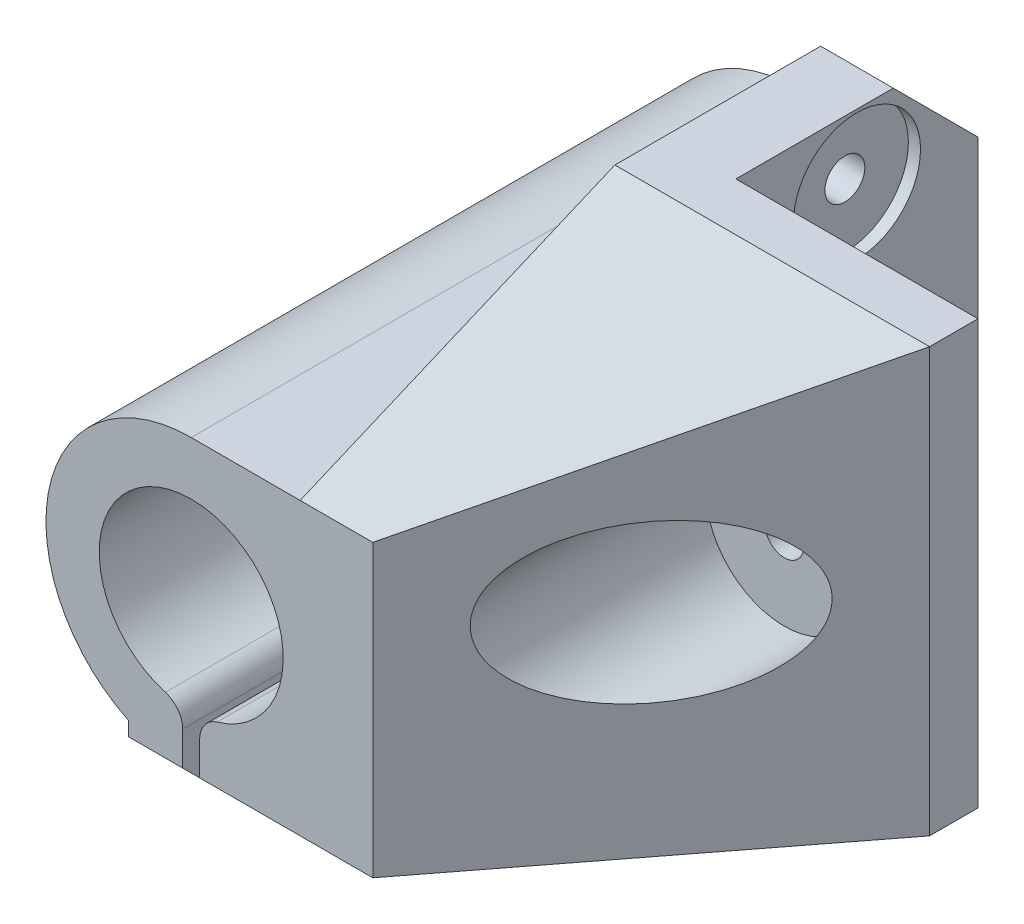
SolidWorks part; units mm, degrees
ref_plane "Plano frontal" through (0, 0, 0) normal (0, 0, 1) x (1, 0, 0)
ref_plane "Plano superior" through (0, 0, 0) normal (0, 1, 0) x (1, 0, 0)
ref_plane "Plano direito" through (0, 0, 0) normal (1, 0, 0) x (0, 0, -1)
sketch "Esboço1" plane through (0, 0, 0) normal (0, 0, 1) x (1, 0, 0)
  line L0 (-10, 11) -> (-10, -24) construction
  line L1 (-35, -24) -> (-35, -31) construction
  line L2 (0, 0) -> (0, 11)
  line L3 (0, -24) -> (0, 0)
  line L4 (-35.7, -19.5677) -> (-35.7, -31)
  line L5 (-34.3, -19.5677) -> (-34.3, -31)
  line L6 (-35, -12) -> (-24.5731, -12) construction
  line L7 (-40.2, -22.8148) -> (-40.2, -31)
  line L8 (-29.8, -24) -> (-29.8, -31)
  line L9 (-34.3, -19.65) -> (-34.3, -31) construction
  line L10 (-26, 0) -> (-35, 0)
  line L12 (-35.7, -19.65) -> (-35.7, -31) construction
  line L13 (-40.2, -19.65) -> (-40.2, -31) construction
  line L14 (-29.8, -19.65) -> (-29.8, -31) construction
  line L15 (-35, -19.65) -> (-35, -31) construction
  line L16 (-29.8, -24) -> (0, -24)
  line L17 (-29.8, -31) -> (-34.3, -31)
  line L18 (-35.7, -31) -> (-40.2, -31)
  line L19 (0, 11) -> (-26, 11)
  line L20 (-26, 11) -> (-26, 0)
  arc A0 (-35, 0) -> (-40.2, -22.8148) centre (-35, -12) ccw
  arc A1 (-34.3, -19.5677) -> (-35.7, -19.5677) centre (-35, -12) ccw
  circle A2 centre (-10, -6.5) radius 1.6
  point P17 (-10, -6.5)
  dimension "D1" = 15.2
  dimension "D5" = 3.2
  dimension "D2" = 35
  dimension "D3" = 24
  dimension "D4" = 10
  dimension "D10" = 7
  dimension "D13" = 11
  dimension "D11" = 9
  dimension "D6" = 0.7
  dimension "D7" = 0.7
  dimension "D8" = 5.2
  dimension "D9" = 5.2
extrude "Ressalto-extrusão1" add sketch "Esboço1" along normal blind 50
sketch "Esboço2" plane through (0, 11, 0) normal (0, 1, 0) x (1, 0, 0)
  line L0 (0, -24) -> (-20, -50)
  line L1 (-20, -50) -> (0, -50)
  line L2 (0, -50) -> (0, -24)
  line L4 (0, -50) -> (0, 0) construction
  line L5 (0, -50) -> (-26, -50) construction
  line L11 (0, 0) -> (-20, 0)
  line L12 (0, 0) -> (0, -20)
  line L13 (0, -20) -> (-20, -20)
  line L14 (-20, 0) -> (-20, -20)
  dimension "D1" = 20
  dimension "D2" = 20
  dimension "D3" = 4
extrude "Corte-extrusão1" cut sketch "Esboço2" against normal through all
sketch "Esboço3" plane through (-26, 0, 0) normal (-1, 0, 0) x (0, 0, 1)
  line L0 (50, -24) -> (43, -31)
  line L1 (50, -31) -> (0, -31) construction
  line L2 (43, -31) -> (50, -31)
  line L3 (0, 0) -> (0, 11) construction
  line L4 (20, -24) -> (20, 11) construction
  line L5 (50, 0) -> (24, 11)
  line L6 (50, -31) -> (50, -24)
  line L7 (50, 11) -> (0, 11) construction
  line L8 (24, 11) -> (50, 11)
  line L9 (50, 11) -> (50, 0)
  line L10 (0, -24) -> (0, -31)
  line L11 (0, -31) -> (7, -31)
  line L12 (7, -31) -> (0, -24)
  line L13 (25, -31) -> (25, -22.8148) construction
  line L14 (50, -22.8148) -> (0, -22.8148) construction
  line L15 (7, 11) -> (0, 4)
  line L16 (0, 4) -> (0, 11)
  line L17 (0, 11) -> (7, 11)
  circle A0 centre (10, 5.5) radius 1.65
  point P6 (0, 5.5)
  point P20 (0, 0)
  point P34 (0, 0)
  dimension "D2" = 3.3
  dimension "D1" = 10
extrude "Corte-extrusão2" cut sketch "Esboço3" against normal through all both and the other way through all
sketch "Esboço4" plane through (0, 0, 50) normal (0, 0, 1) x (1, 0, 0)
  circle A0 centre (-10, -6.5) radius 6.5
  dimension "D1" = 13
sketch "Esboço6" plane through (-29.8, 0, 0) normal (1, 0, 0) x (0, 0, -1)
  line L1 (-50, -31) -> (-50, -24) construction
  line L2 (-25, -31) -> (-25, -24) construction
  line L3 (-43, -31) -> (-7, -31) construction
  line L4 (-50, -24) -> (0, -24) construction
  circle A0 centre (-38, -27.5) radius 1.65
  circle A1 centre (-12, -27.5) radius 1.65
  point P9 (-50, -27.5)
  dimension "D1" = 3.3
  dimension "D2" = 12
extrude "Corte-extrusão4" cut sketch "Esboço6" against normal through all
fillet "Filete1" radius 2 2 edges at (-35.7, -19.5677, 25) (-34.3, -19.5677, 25)
extrude "Corte-extrusão5" cut sketch "Esboço4" against normal offset from surface (24 mm away) 6 up to face at (-8.4, -6.5, 20)
sketch "Esboço7" plane through (-29.8, 0, 0) normal (1, 0, 0) x (0, 0, -1)
  line L1 (-8.8246, -27.5) -> (-10.4123, -24.75)
  line L2 (-10.4123, -24.75) -> (-13.5877, -24.75)
  line L3 (-13.5877, -24.75) -> (-15.1754, -27.5)
  line L4 (-15.1754, -27.5) -> (-13.5877, -30.25)
  line L5 (-13.5877, -30.25) -> (-10.4123, -30.25)
  line L6 (-10.4123, -30.25) -> (-8.8246, -27.5)
  line L7 (-34.8246, -27.5) -> (-36.4123, -24.75)
  line L8 (-36.4123, -24.75) -> (-39.5877, -24.75)
  line L9 (-39.5877, -24.75) -> (-41.1754, -27.5)
  line L10 (-41.1754, -27.5) -> (-39.5877, -30.25)
  line L11 (-39.5877, -30.25) -> (-36.4123, -30.25)
  line L12 (-36.4123, -30.25) -> (-34.8246, -27.5)
  circle A0 centre (-12, -27.5) radius 2.75 construction
  circle A1 centre (-38, -27.5) radius 2.75 construction
  dimension "D1" = 5.5
extrude "Corte-extrusão6" cut sketch "Esboço7" against normal blind 1
sketch "Esboço8" plane through (-20, 0, 0) normal (1, 0, 0) x (0, 0, -1)
  circle A0 centre (-10, 5.5) radius 5.25
  dimension "D1" = 10.5
extrude "Corte-extrusão7" cut sketch "Esboço8" against normal blind 1
sketch "Esboço9" plane through (0, 0, 20) normal (0, 0, -1) x (-1, 0, 0)
  circle A0 centre (10, -6.5) radius 5.25
  dimension "D1" = 10.5
extrude "Corte-extrusão8" cut sketch "Esboço9" against normal blind 1
equation "\"D9@Esboço1\"=\"D8@Esboço1\""
